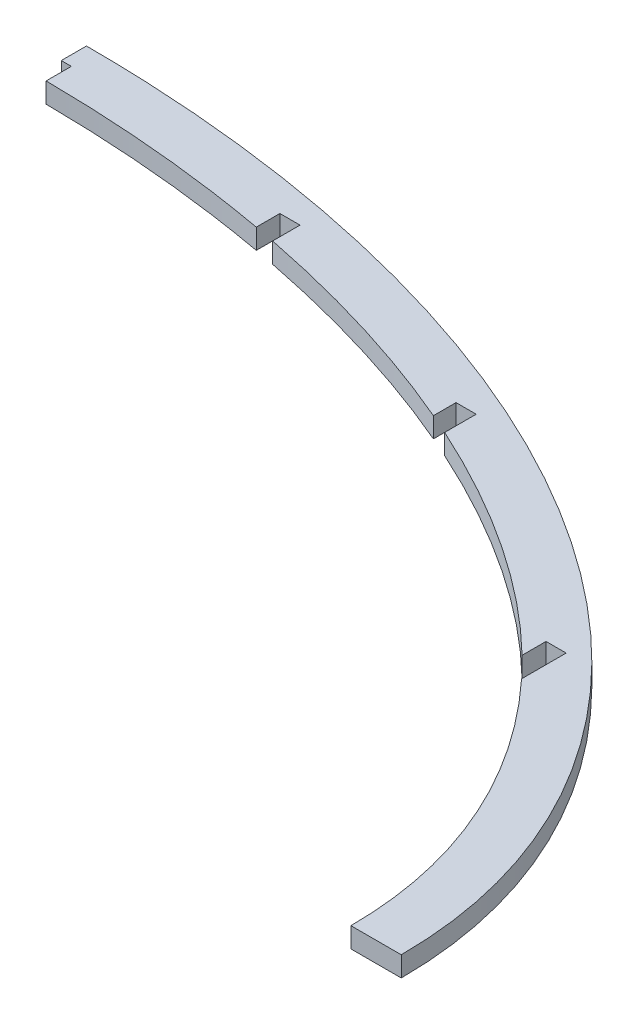
SolidWorks part; units mm, degrees
ref_plane "Спереди" through (0, 0, 0) normal (0, 0, 1) x (1, 0, 0)
ref_plane "Сверху" through (0, 0, 0) normal (0, 1, 0) x (1, 0, 0)
ref_plane "Справа" through (0, 0, 0) normal (1, 0, 0) x (0, 0, -1)
other "Configuration Table"
sketch "Эскиз1" plane through (0, 0, 0) normal (0, 1, 0) x (1, 0, 0)
  line L0 (-1000, 500) -> (-1000, 480)
  line L1 (-1710, 0) -> (-1600, 0) construction
  line L2 (-290, 0) -> (-250, 0)
  line L8 (-1750, 0) -> (-1600, 0) construction
  line L9 (-1000, 480) -> (-992, 480)
  line L11 (-992, 480) -> (-992, 459.9708)
  line L12 (-808, 461.62) -> (-792, 461.62)
  line L13 (-808, 461.62) -> (-808, 442.8612)
  line L14 (-792, 461.62) -> (-792, 439.8177)
  line L15 (-608, 401.5) -> (-592, 401.5)
  line L16 (-608, 401.5) -> (-608, 383.534)
  line L17 (-592, 401.5) -> (-592, 376.4644)
  line L18 (-408, 272.97) -> (-392, 272.97)
  line L19 (-408, 272.97) -> (-408, 253.9487)
  line L20 (-392, 272.97) -> (-392, 237.5512)
  line L22 (-1000, 0) -> (-290, 0) construction
  line L23 (-1000, 0) -> (-290, 0) construction
  ellipse E0 centre (-1000, 0) end of major axis (-290, 0) minor radius 460 (-290, 0) -> (-392, 237.5512) ccw
  ellipse E1 centre (-1000, 0) end of major axis (-1750, 0) minor radius 500 (-250, 0) -> (-1000, 500) ccw
  ellipse E2 centre (-1000, 0) end of major axis (-290, 0) minor radius 460 (-808, 442.8612) -> (-992, 459.9708) ccw
  ellipse E3 centre (-1000, 0) end of major axis (-290, 0) minor radius 460 (-608, 383.534) -> (-792, 439.8177) ccw
  ellipse E4 centre (-1000, 0) end of major axis (-290, 0) minor radius 460 (-408, 253.9487) -> (-592, 376.4644) ccw
  dimension "D1" = 920
  dimension "D2" = 1420
  dimension "D12" = 1000
  dimension "D13" = 1500
  dimension "D18" = 480
  dimension "D19" = 16
  dimension "D21" = 461.62
  dimension "D22" = 16
  dimension "D24" = 401.5
  dimension "D25" = 16
  dimension "D27" = 272.97
extrude "Бобышка-Вытянуть1" add sketch "Эскиз1" along normal blind 16
